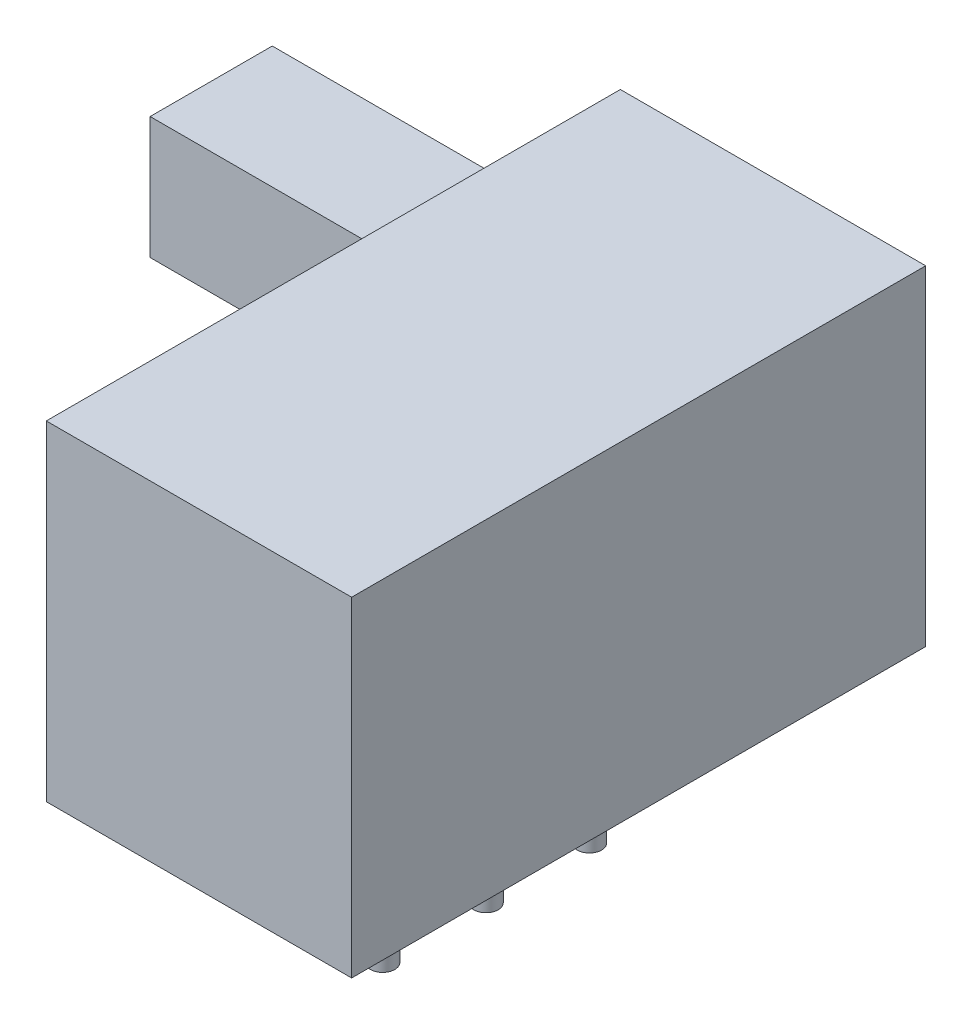
SolidWorks part; units mm, degrees
ref_plane "Front Plane" through (0, 0, 0) normal (0, 0, 1) x (1, 0, 0)
ref_plane "Top Plane" through (0, 0, 0) normal (0, 1, 0) x (1, 0, 0)
ref_plane "Right Plane" through (0, 0, 0) normal (1, 0, 0) x (0, 0, -1)
sketch "Sketch1" plane through (0, 0, 0) normal (0, 1, 0) x (1, 0, 0)
  circle A0 centre (0, 0) radius 0.3
  circle A1 centre (0, -2.54) radius 0.3
  circle A2 centre (0, 2.54) radius 0.3
  point P7 (0, 0)
  dimension "D1" = 0.6
  dimension "D2" = 2.54
  dimension "D3" = 2.54
extrude "Boss-Extrude1" add sketch "Sketch1" against normal blind 3.8
sketch "Sketch2" plane through (0, 0, 0) normal (0, 1, 0) x (1, 0, 0)
  line L1 (3.75, 7.05) -> (-3.75, 7.05)
  line L2 (3.75, 7.05) -> (3.75, -7.05)
  line L3 (3.75, -7.05) -> (-3.75, -7.05)
  line L4 (-3.75, 7.05) -> (-3.75, -7.05)
  line L5 (3.75, 7.05) -> (-3.75, -7.05) construction
  line L6 (3.75, -7.05) -> (-3.75, 7.05) construction
  point P0 (0, 0)
  dimension "D1" = 7.5
  dimension "D2" = 14.1
extrude "Boss-Extrude2" add sketch "Sketch2" along normal blind 8.1
sketch "Sketch3" plane through (-3.75, 0, 0) normal (-1, 0, 0) x (0, 0, 1)
  line L1 (-4.5, 7.3) -> (-1.5, 7.3)
  line L2 (-4.5, 7.3) -> (-4.5, 4.3)
  line L3 (-4.5, 4.3) -> (-1.5, 4.3)
  line L4 (-1.5, 7.3) -> (-1.5, 4.3)
  line L5 (-7.05, 0) -> (7.05, 0) construction
  point P6 (-3, 4.3)
  dimension "D1" = 3
  dimension "D2" = 4.3
  dimension "D3" = 3
extrude "Boss-Extrude3" add sketch "Sketch3" along normal blind 6
equation "\"D3@Sketch1\"=\"D2@Sketch1\""
